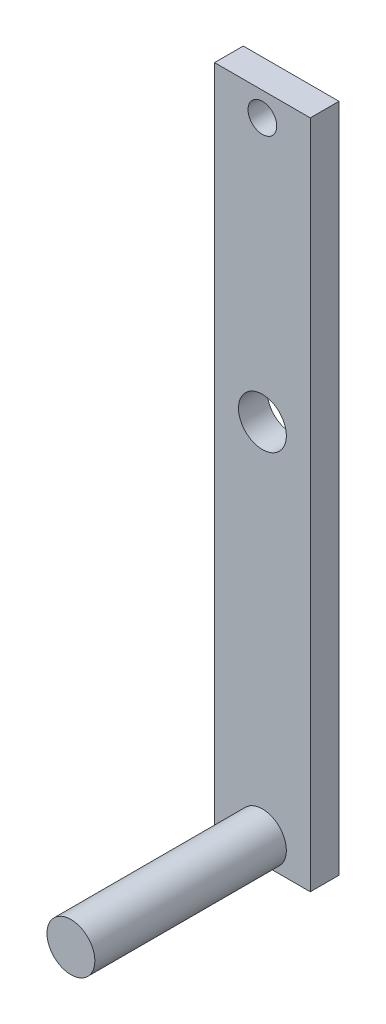
SolidWorks part; units mm, degrees
ref_plane "Front Plane" through (0, 0, 0) normal (0, 0, 1) x (1, 0, 0)
ref_plane "Top Plane" through (0, 0, 0) normal (0, 1, 0) x (1, 0, 0)
ref_plane "Right Plane" through (0, 0, 0) normal (1, 0, 0) x (0, 0, -1)
sketch "Sketch1" plane through (0, 0, 0) normal (0, 0, 1) x (1, 0, 0)
  line L1 (0, 0) -> (10, 0)
  line L2 (0, 0) -> (0, 70)
  line L3 (0, 70) -> (10, 70)
  line L4 (10, 0) -> (10, 70)
  dimension "D1" = 70
  dimension "D2" = 10
extrude "Boss-Extrude1" add sketch "Sketch1" along normal blind 3
sketch "Sketch2" plane through (0, 0, 3) normal (0, 0, 1) x (1, 0, 0)
  line L3 (0, 0) -> (10, 0) construction
  circle A0 centre (5, 2.5) radius 2.5
  point P4 (5, 0)
  dimension "D1" = 2.5
  dimension "D2" = 5
extrude "Boss-Extrude2" add sketch "Sketch2" along normal blind 20
sketch "Sketch3" plane through (0, 0, 0) normal (0, 0, -1) x (-1, 0, 0)
  line L0 (0, 0) -> (-10, 0) construction
  line L3 (0, 70) -> (0, 0) construction
  circle A0 centre (-5, 40) radius 2.5
  dimension "D2" = 5
  dimension "D1" = 40
  dimension "D3" = 5
sketch "Sketch4" plane through (0, 0, 0) normal (0, 0, -1) x (-1, 0, 0)
  line L1 (-10, 70) -> (0, 70) construction
  circle A0 centre (-5, 67.5) radius 1.5
  point P2 (0, 0)
  point P5 (-5, 70)
  dimension "D1" = 3
  dimension "D2" = 2.5
extrude "Cut-Extrude1" cut sketch "Sketch4" against normal blind 20
extrude "Cut-Extrude3" cut sketch "Sketch3" against normal blind 20
